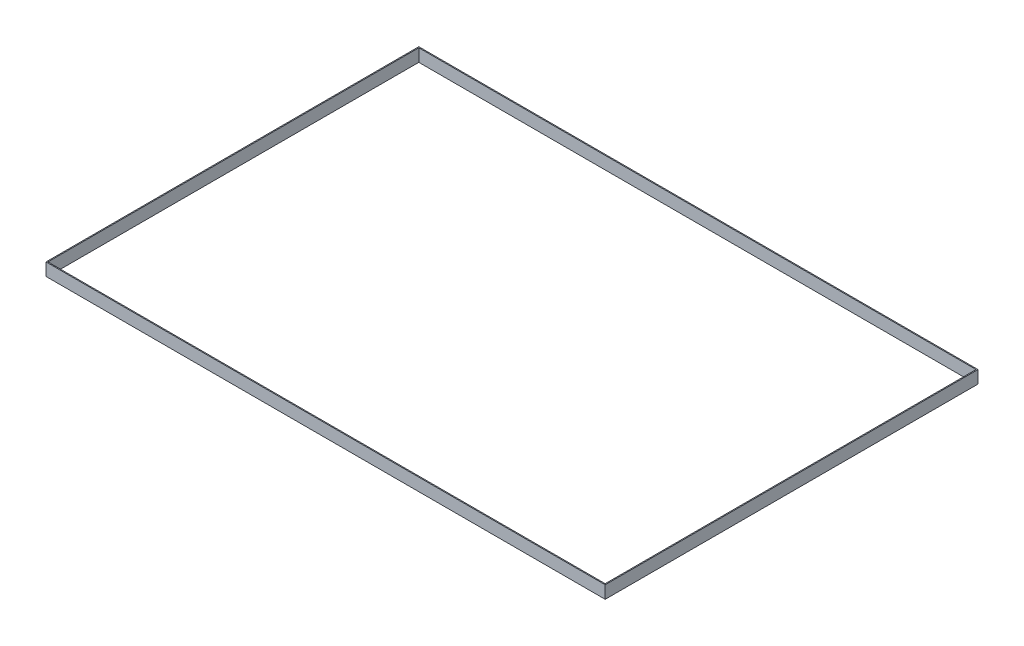
SolidWorks part; units mm, degrees
ref_plane "Front Plane" through (0, 0, 0) normal (0, 0, 1) x (1, 0, 0)
ref_plane "Top Plane" through (0, 0, 0) normal (0, 1, 0) x (1, 0, 0)
ref_plane "Right Plane" through (0, 0, 0) normal (1, 0, 0) x (0, 0, -1)
sketch "Sketch1" plane through (0, 0, 0) normal (0, 1, 0) x (1, 0, 0)
  line L1 (0, 0) -> (3657.6, 0)
  line L2 (0, 0) -> (0, 2438.4)
  line L3 (0, 2438.4) -> (3657.6, 2438.4)
  line L4 (3657.6, 0) -> (3657.6, 2438.4)
  dimension "D1" = 2438.4
  dimension "D2" = 3657.6
extrude "Boss-Extrude1" add sketch "Sketch1" along normal blind 6.35
sketch "Sketch3" plane through (0, 6.35, 0) normal (0, 1, 0) x (1, 0, 0)
  line L0 (0, 2438.4) -> (0, 0) construction
  line L1 (6.35, 2432.05) -> (3651.25, 2432.05)
  line L2 (6.35, 2432.05) -> (6.35, 6.35)
  line L3 (6.35, 6.35) -> (3651.25, 6.35)
  line L4 (3651.25, 2432.05) -> (3651.25, 6.35)
  line L5 (0, 0) -> (3657.6, 0) construction
  line L6 (3657.6, 0) -> (3657.6, 2438.4) construction
  line L7 (3657.6, 2438.4) -> (0, 2438.4) construction
  line L9 (0, 2438.4) -> (3657.6, 2438.4)
  line L10 (0, 2438.4) -> (0, 0)
  line L11 (0, 0) -> (3657.6, 0)
  line L12 (3657.6, 2438.4) -> (3657.6, 0)
  dimension "D1" = 6.35
  dimension "D2" = 6.35
  dimension "D3" = 6.35
  dimension "D4" = 6.35
extrude "Boss-Extrude2" add sketch "Sketch3" along normal blind 76.2
sketch "Sketch4" plane through (0, 6.35, 0) normal (0, 1, 0) x (1, 0, 0)
  line L0 (6.35, 6.35) -> (3651.25, 6.35) construction
  line L1 (6.35, 2432.05) -> (3651.25, 2432.05)
  line L2 (6.35, 2432.05) -> (6.35, 6.35)
  line L3 (6.35, 6.35) -> (3651.25, 6.35)
  line L4 (3651.25, 2432.05) -> (3651.25, 6.35)
  line L5 (3651.25, 6.35) -> (3651.25, 2432.05) construction
extrude "Cut-Extrude1" cut sketch "Sketch4" against normal through all
